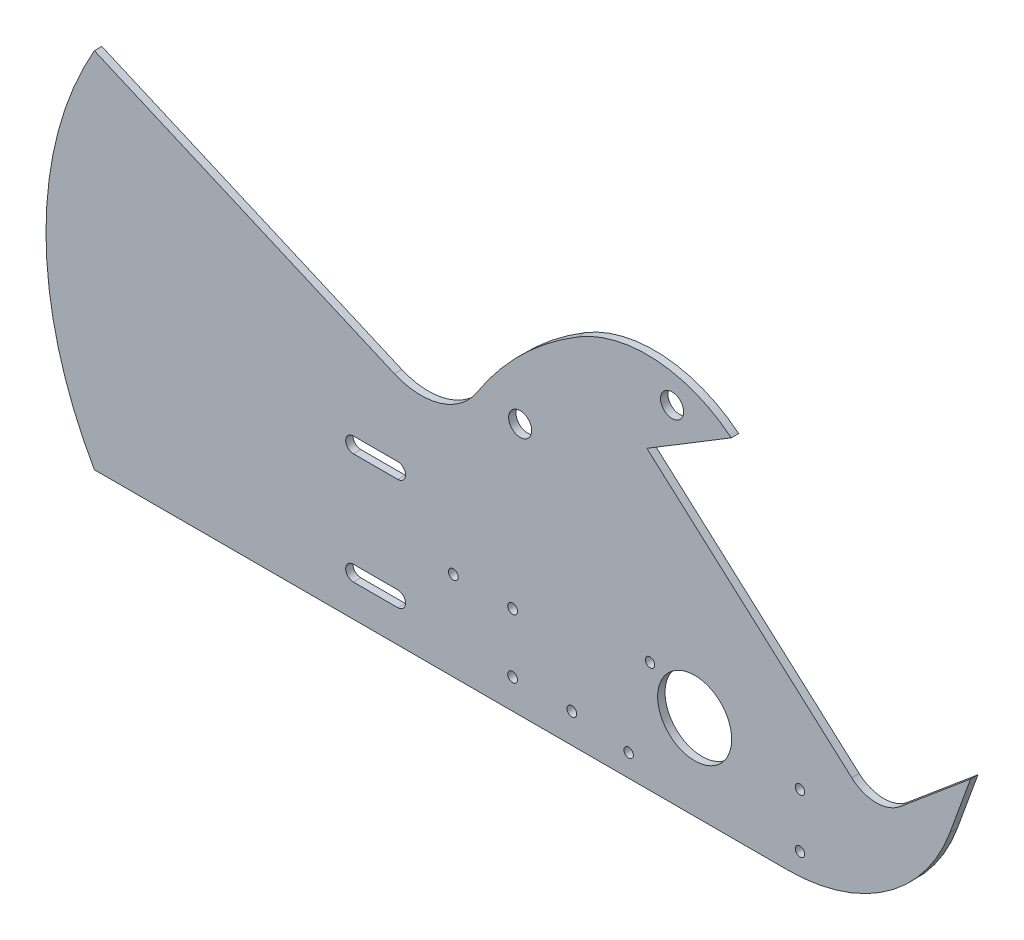
SolidWorks part; units mm, degrees
ref_plane "Front Plane" through (0, 0, 0) normal (0, 0, 1) x (1, 0, 0)
ref_plane "Top Plane" through (0, 0, 0) normal (0, 1, 0) x (1, 0, 0)
ref_plane "Right Plane" through (0, 0, 0) normal (1, 0, 0) x (0, 0, -1)
sketch "Sketch1" plane through (0, 0, 0) normal (0, 0, 1) x (1, 0, 0)
  line L0 (-127.5854, -38.9313) -> (20.8959, -38.9313)
  line L1 (-69.2519, 114.0082) -> (48.2932, 9.0757) construction
  line L2 (-123.4547, 50.5236) -> (-177.3723, 73.8446) construction
  line L3 (-177.3723, 73.8446) -> (-276.4514, 116.6993)
  line L4 (-127.5854, -38.9313) -> (-276.4514, -38.9313)
  line L5 (-3.3407, 109.4664) -> (-39.5357, 87.4805)
  line L6 (-49.472, 81.4449) -> (-39.5357, 87.4805) construction
  line L7 (48.2932, 9.0757) -> (-39.5357, 87.4805)
  line L8 (69.0694, 8.7574) -> (99.264, 34.0937)
  line L9 (99.264, 34.0937) -> (90.398, 9.7346)
  line L10 (-177.3723, 73.8446) -> (-147.787, 61.0481)
  arc A0 (-91.9293, -25.095) -> (-49.472, 81.4449) centre (0, 0) cw construction
  arc A1 (-123.4547, 50.5236) -> (-69.2519, 114.0082) centre (0, 0) cw construction
  arc A2 (-276.4514, 116.6993) -> (-276.4514, -38.9313) centre (-140.7857, 38.884) ccw
  arc A3 (-69.2519, 114.0082) -> (-3.3407, 109.4664) centre (-39.5134, 65.0502) cw
  arc A4 (20.8959, -38.9313) -> (90.398, 9.7346) centre (20.8959, 35.0313) ccw
  arc A5 (69.0694, 8.7574) -> (48.2932, 9.0757) centre (58.8652, 20.9184) cw
  arc A6 (-147.787, 61.0481) -> (-112.3713, 71.8775) centre (-136.4431, 87.2749) ccw
  arc A7 (-112.3713, 71.8775) -> (-69.2519, 114.0082) centre (0, 0) cw
  point P0 (-49.472, 81.4449)
  point P1 (-88.476, 35.3942)
  point P3 (-91.9293, -25.095)
  dimension "D3" = 42.3492
  dimension "D4" = 73.025
  dimension "D5" = 40
  dimension "D7" = 15.875
  dimension "D8" = 95.293
  dimension "D9" = 133.393
  dimension "D10" = 57.2823
  dimension "D11" = 73.9626
  dimension "D24" = 28.575
  dimension "D2" = 53.975
  dimension "D6" = 30
  dimension "D12" = 20.8959
  dimension "D13" = 48.2932
  dimension "D14" = 58.8652
  dimension "D15" = 3.3407
  dimension "D16" = 39.5134
  dimension "D17" = 39.5357
  dimension "D18" = 88.476
  dimension "D19" = 91.9293
  dimension "D20" = 123.4547
  dimension "D21" = 140.7857
  dimension "D22" = 177.3723
  dimension "D23" = 8.7574
  dimension "D25" = 107.95
extrude "Boss-Extrude1" add sketch "Sketch1" along normal blind 3.175
sketch "Sketch4" plane through (0, 0, 0) normal (0, 0, 1) x (1, 0, 0)
  line L0 (-276.4514, -38.9313) -> (20.8959, -38.9313) construction
  circle A0 centre (-19.051, -2.4188) radius 15.875
  dimension "D1" = 31.75
  dimension "D2" = 36.5125
  dimension "D3" = 19.051
extrude "Cut-Extrude1" cut sketch "Sketch4" along normal through all
sketch "Sketch8" plane through (0, 0, 3.175) normal (0, 0, 1) x (1, 0, 0)
  line L0 (-276.4514, -38.9313) -> (20.8959, -38.9313) construction
  circle A0 centre (-229.6905, 15.5417) radius 2.7559
  arc A3 (-265.6115, 51.4627) -> (-265.6115, -20.3793) centre (-229.6905, 15.5417) ccw construction
  arc A4 (-267.5603, 53.4114) -> (-267.5603, -22.328) centre (-229.6905, 15.5417) ccw
  arc A5 (-263.6628, 49.514) -> (-263.6628, -18.4306) centre (-229.6905, 15.5417) ccw
  arc A6 (-263.6628, 49.514) -> (-267.5603, 53.4114) centre (-265.6115, 51.4627) ccw
  arc A7 (-267.5603, -22.328) -> (-263.6628, -18.4306) centre (-265.6115, -20.3793) ccw
  arc A9 (-247.651, 33.5022) -> (-247.651, -2.4188) centre (-229.6905, 15.5417) ccw construction
  arc A10 (-254.3862, 40.2374) -> (-254.3862, -9.154) centre (-229.6905, 15.5417) ccw
  arc A11 (-240.9158, 26.767) -> (-240.9158, 4.3164) centre (-229.6905, 15.5417) ccw
  arc A12 (-240.9158, 26.767) -> (-254.3862, 40.2374) centre (-247.651, 33.5022) ccw
  arc A13 (-254.3862, -9.154) -> (-240.9158, 4.3164) centre (-247.651, -2.4188) ccw
  point P11 (-280.4905, 15.5417)
  point P20 (-255.0905, 15.5417)
  dimension "D2" = 50.8
  dimension "D5" = 328.9545
  dimension "D1" = 5.5118
  dimension "D3" = 25.4
  dimension "D4" = 34.925
  dimension "D6" = 16.6033
extrude "Cut-Extrude2" [suppressed] cut sketch "Sketch8" against normal through all
sketch "Sketch9" plane through (0, 0, 3.175) normal (0, 0, 1) x (1, 0, 0)
  line L0 (-276.4514, -38.9313) -> (-101.8264, -38.9313)
  line L2 (-276.4514, 116.6993) -> (-147.787, 61.0481)
  line L3 (-276.4514, -38.9313) -> (20.8959, -38.9313) construction
  arc A0 (-101.8264, -38.9313) -> (-126.3148, -20.275) centre (-101.8264, -13.5313) cw
  arc A1 (-276.4514, 116.6993) -> (-276.4514, -38.9313) centre (-168.1072, 38.884) ccw
  arc A2 (-147.787, 61.0481) -> (-112.3713, 71.8775) centre (-136.4431, 87.2749) ccw construction
  arc A3 (-126.3148, -20.275) -> (-112.3713, 71.8775) centre (-15.8572, 10.1429) cw
  arc A4 (-147.787, 61.0481) -> (-112.3713, 71.8775) centre (-136.4431, 87.2749) ccw
  arc A6 (-69.2519, 114.0082) -> (-112.3713, 71.8775) centre (0, 0) ccw construction
  dimension "D1" = 133.393
  dimension "D3" = 174.625
  dimension "D2" = 25.4
extrude "Cut-Extrude3" [suppressed] cut sketch "Sketch9" against normal through all
sketch "Sketch10" plane through (0, 0, 3.175) normal (0, 0, 1) x (1, 0, 0)
  line L0 (-276.4514, -38.9313) -> (20.8959, -38.9313) construction
  circle A0 centre (-97.1144, -26.2313) radius 2.0955
  circle A1 centre (-71.7144, -26.2313) radius 2.0955
  circle A2 centre (-122.5144, -0.8313) radius 2.0955
  circle A3 centre (-97.1144, -0.8313) radius 2.0955
  dimension "D1" = 4.191
  dimension "D2" = 71.7144
  dimension "D3" = 97.1144
  dimension "D4" = 122.5144
  dimension "D5" = 12.7
  dimension "D6" = 25.4
extrude "Cut-Extrude5" cut sketch "Sketch10" against normal through all
sketch "Sketch11" plane through (0, 0, 3.175) normal (0, 0, 1) x (1, 0, 0)
  line L0 (-165.3872, -25.0883) -> (-146.3372, -25.0883) construction
  line L1 (-165.3872, -18.4843) -> (-146.3372, -18.4843) construction
  line L2 (-165.3872, 29.1407) -> (-146.3372, 29.1407) construction
  line L3 (-165.3872, 22.5367) -> (-146.3372, 22.5367) construction
  line L4 (-165.3872, -25.0883) -> (-146.3372, -25.0883)
  line L5 (-165.3872, -18.4843) -> (-146.3372, -18.4843)
  line L6 (-165.3872, 29.1407) -> (-146.3372, 29.1407)
  line L7 (-165.3872, 22.5367) -> (-146.3372, 22.5367)
  arc A0 (-146.3372, -25.0883) -> (-146.3372, -18.4843) centre (-146.3372, -21.7863) ccw construction
  arc A1 (-165.3872, -18.4843) -> (-165.3872, -25.0883) centre (-165.3872, -21.7863) ccw construction
  arc A2 (-146.3372, 22.5367) -> (-146.3372, 29.1407) centre (-146.3372, 25.8387) ccw construction
  arc A3 (-165.3872, 29.1407) -> (-165.3872, 22.5367) centre (-165.3872, 25.8387) ccw construction
  arc A4 (-146.3372, -25.0883) -> (-146.3372, -18.4843) centre (-146.3372, -21.7863) ccw
  arc A5 (-165.3872, -18.4843) -> (-165.3872, -25.0883) centre (-165.3872, -21.7863) ccw
  arc A6 (-146.3372, 22.5367) -> (-146.3372, 29.1407) centre (-146.3372, 25.8387) ccw
  arc A7 (-165.3872, 29.1407) -> (-165.3872, 22.5367) centre (-165.3872, 25.8387) ccw
extrude "Cut-Extrude6" cut sketch "Sketch11" against normal up to surface (3.175 mm away) up to face at (-69.6189, -26.2313, 0)
sketch "Sketch12" plane through (0, 0, 3.175) normal (0, 0, 1) x (1, 0, 0)
  circle A0 centre (26.1116, -6.3306) radius 2.0193 construction
  circle A1 centre (-38.1909, 8.6937) radius 2.0193 construction
  circle A2 centre (-47.3544, -29.4063) radius 2.0193 construction
  circle A3 centre (26.1116, -29.4063) radius 2.0193 construction
  circle A4 centre (26.1116, -6.3306) radius 2.0193
  circle A5 centre (-38.1909, 8.6937) radius 2.0193
  circle A6 centre (-47.3544, -29.4063) radius 2.0193
  circle A7 centre (26.1116, -29.4063) radius 2.0193
extrude "Cut-Extrude7" cut sketch "Sketch12" against normal up to surface (3.175 mm away) up to face at (-155.8622, 25.8387, 0)
hole_wizard "25/64 (0.39063) Diameter Hole1" positions "Sketch13" profile "Sketch14" hole size "25/64" standard "ANSI Inch" end condition through all
sketch "Sketch13" plane through (0, 0, 3.175) normal (0, 0, 1) x (1, 0, 0)
  line L0 (-93.8673, 69.3373) -> (-28.7407, 108.8971) construction
  line L2 (-39.5357, 87.4805) -> (-3.3407, 109.4664) construction
  point P0 (-28.7407, 108.8971)
  point P2 (-93.8673, 69.3373)
  dimension "D1" = 76.2
  dimension "D2" = 12.7
  dimension "D3" = 25.4
sketch "Sketch14" plane through (-28.7407, 108.8971, 3.175) normal (1, 0, 0) x (0, -1, 0)
  line L0 (0, 0) -> (0, 3.175)
  line L1 (0, 3.175) -> (4.961, 3.175)
  line L2 (4.961, 3.175) -> (4.961, 0)
  line L5 (4.961, 0) -> (0, 0)
  line L11 (0, -6.35) -> (0, 107.95) construction
  dimension "Thru Hole Dia." = 9.922
  dimension "Thru Hole Depth" = 3.175
sketch "Sketch15" [suppressed] plane through (0, 0, 3.175) normal (0, 0, 1) x (1, 0, 0)
  line L0 (-276.4514, -38.9313) -> (20.8959, -38.9313) construction
  circle A0 centre (-63.5, -8.4513) radius 4.953
  circle A1 centre (-203.2, 37.2687) radius 4.953
  dimension "D1" = 9.906
  dimension "D2" = 9.906
  dimension "D3" = 76.2
  dimension "D4" = 203.2
  dimension "D5" = 30.48
  dimension "D6" = 63.5
extrude "Cut-Extrude8" [suppressed] cut sketch "Sketch15" against normal through all
